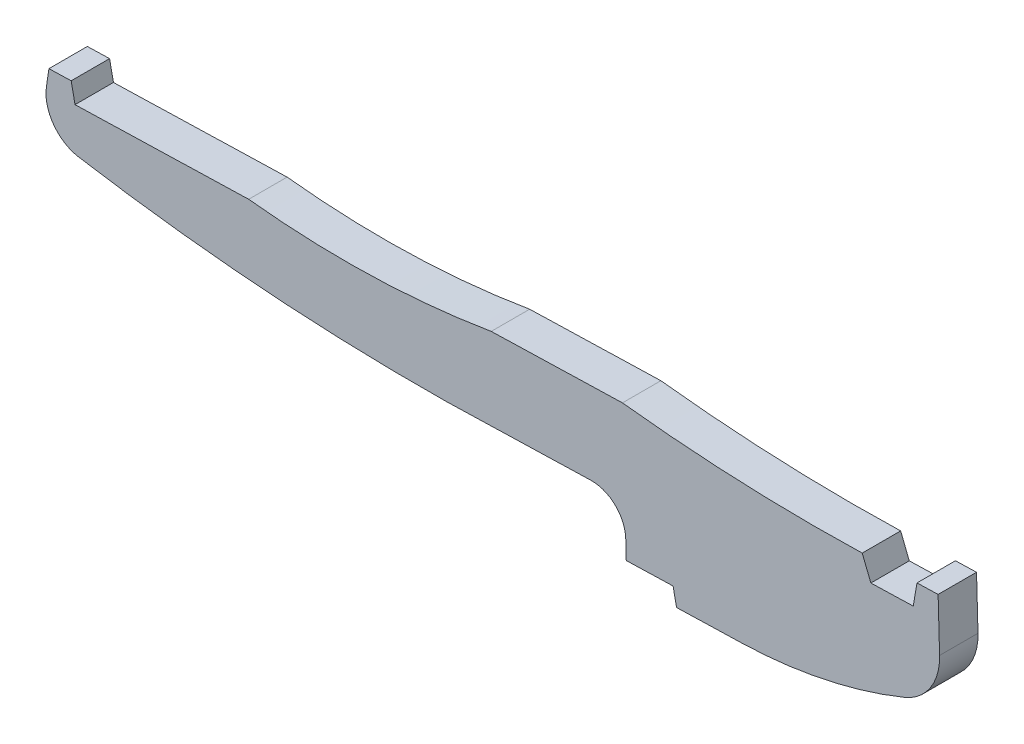
SolidWorks part; units mm, degrees
ref_plane "Front Plane" through (0, 0, 0) normal (0, 0, 1) x (1, 0, 0)
ref_plane "Top Plane" through (0, 0, 0) normal (0, 1, 0) x (1, 0, 0)
ref_plane "Right Plane" through (0, 0, 0) normal (1, 0, 0) x (0, 0, -1)
sketch "Sketch1" plane through (0, 0, 0) normal (0, 0, 1) x (1, 0, 0)
  line L0 (-3.7366, -0.1055) -> (0, 0)
  line L1 (-61.4591, -13.2394) -> (-86.9528, -13.9591)
  line L2 (-55.1979, -22.4089) -> (-55.2922, -19.0678)
  line L3 (-46.91, -22.1749) -> (-55.1979, -22.4089)
  line L4 (-46.2966, -25.1588) -> (-46.91, -22.1749)
  line L5 (-34.7871, -24.8339) -> (-46.2966, -25.1588)
  line L6 (0, 0) -> (0.2604, -9.2252)
  line L7 (-4.4061, -3.9941) -> (-3.7366, -0.1055)
  line L8 (-11.9031, -4.2057) -> (-4.4061, -3.9941)
  line L9 (-13.4323, -0.3792) -> (-11.9031, -4.2057)
  line L10 (-79.0983, 0.7684) -> (-55.8707, 1.4241)
  line L11 (-157.3907, 1.8983) -> (-153.4502, 2.0095)
  line L12 (-157.8348, -1.1154) -> (-157.3907, 1.8983)
  line L13 (-152.7676, -1.3111) -> (-122.0281, -0.4434)
  line L14 (-153.4502, 2.0095) -> (-152.7676, -1.3111)
  arc A0 (-55.2922, -19.0678) -> (-61.4591, -13.2394) centre (-61.2898, -19.2371) ccw
  arc A1 (-5.9656, -18.7695) -> (0.2604, -9.2252) centre (-9.7356, -9.5074) ccw
  arc A2 (-34.7871, -24.8339) -> (-5.9656, -18.7695) centre (-37.1187, 57.7677) ccw
  arc A3 (-55.8707, 1.4241) -> (-13.4323, -0.3792) centre (-21.9174, 300.2119) ccw
  arc A4 (-122.0281, -0.4434) -> (-79.0983, 0.7684) centre (-104.9146, 154.3162) ccw
  arc A5 (-157.8348, -1.1154) -> (-152.3973, -8.9761) centre (-150.9096, -2.136) ccw
  arc A6 (-152.3973, -8.9761) -> (-86.9528, -13.9591) centre (-91.4578, 359.1231) ccw
extrude "Boss-Extrude1" add sketch "Sketch1" along normal blind 6.8
